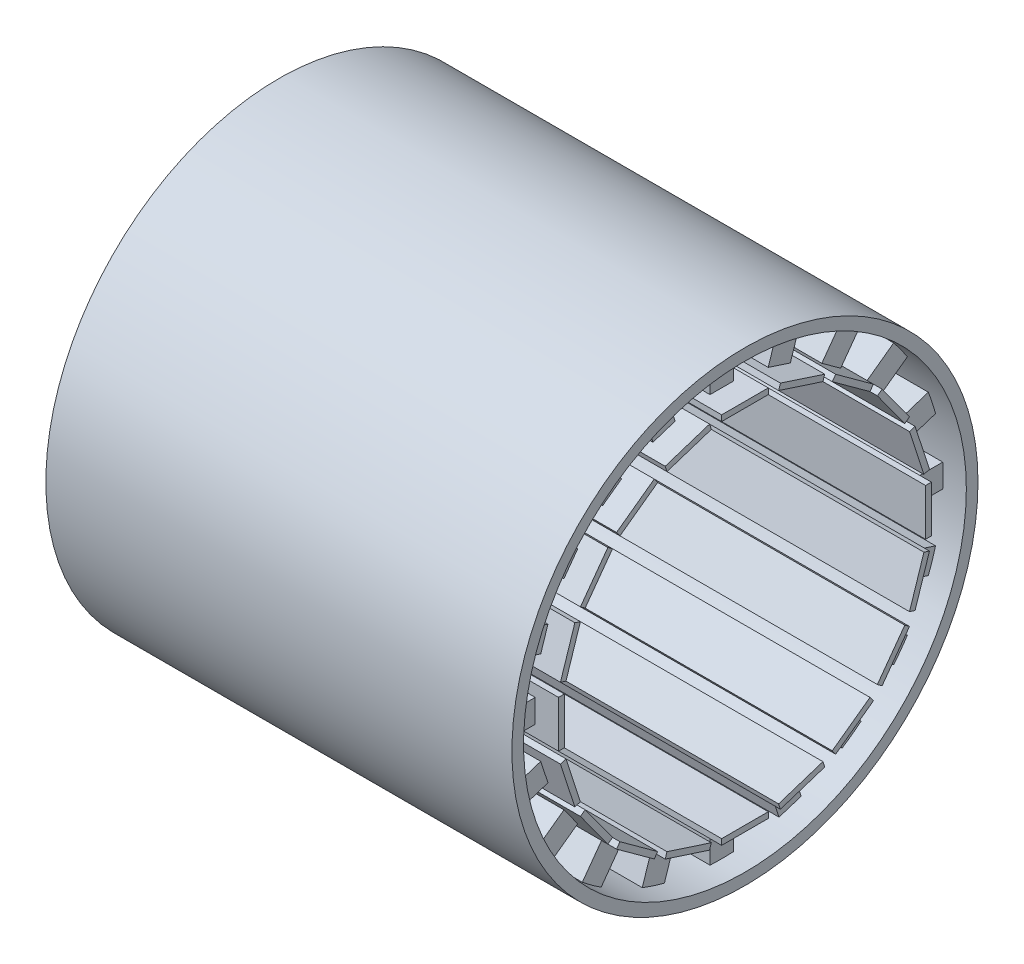
SolidWorks part; units mm, degrees
ref_plane "Front Plane" through (0, 0, 0) normal (0, 0, 1) x (1, 0, 0)
ref_plane "Top Plane" through (0, 0, 0) normal (0, 1, 0) x (1, 0, 0)
ref_plane "Right Plane" through (0, 0, 0) normal (1, 0, 0) x (0, 0, -1)
sketch "Sketch2" plane through (0, 0, 0) normal (1, 0, 0) x (0, 0, -1)
  circle A0 centre (0, 0) radius 50.8
  circle A1 centre (0, 0) radius 48.26
  dimension "D1" = 101.6
  dimension "D2" = 96.52
extrude "Boss-Extrude1" add sketch "Sketch2" along normal mid plane 101.6
sketch "Sketch3" plane through (0, 0, 0) normal (1, 0, 0) x (0, 0, -1)
  line L1 (-2.54, -40.64) -> (2.54, -40.64)
  line L2 (-2.54, -40.64) -> (-2.54, -48.26)
  line L3 (-2.54, -48.26) -> (2.54, -48.26)
  line L4 (2.54, -40.64) -> (2.54, -48.26)
  line L5 (-2.54, -40.64) -> (2.54, -48.26) construction
  line L6 (-2.54, -48.26) -> (2.54, -40.64) construction
  circle A0 centre (0, 0) radius 48.26 construction
  point P0 (0, -44.45)
  dimension "D1" = 7.62
  dimension "D2" = 5.08
extrude "Boss-Extrude2" add sketch "Sketch3" along normal mid plane 91.44
sketch "Sketch4" plane through (0, -40.64, 0) normal (0, 1, 0) x (1, 0, 0)
  line L1 (-50.8, -5.08) -> (50.8, -5.08)
  line L2 (-50.8, -5.08) -> (-50.8, 5.08)
  line L3 (-50.8, 5.08) -> (50.8, 5.08)
  line L4 (50.8, -5.08) -> (50.8, 5.08)
  line L5 (-50.8, -5.08) -> (50.8, 5.08) construction
  line L6 (-50.8, 5.08) -> (50.8, -5.08) construction
  point P0 (0, 0)
  dimension "D1" = 101.6
  dimension "D2" = 10.16
extrude "Boss-Extrude3" add sketch "Sketch4" along normal blind 1.27
pattern_circular "CirPattern1" count 20 over 360 about axis through (0, 0, 0) along (1, 0, 0) of "Boss-Extrude3", "Boss-Extrude2"
